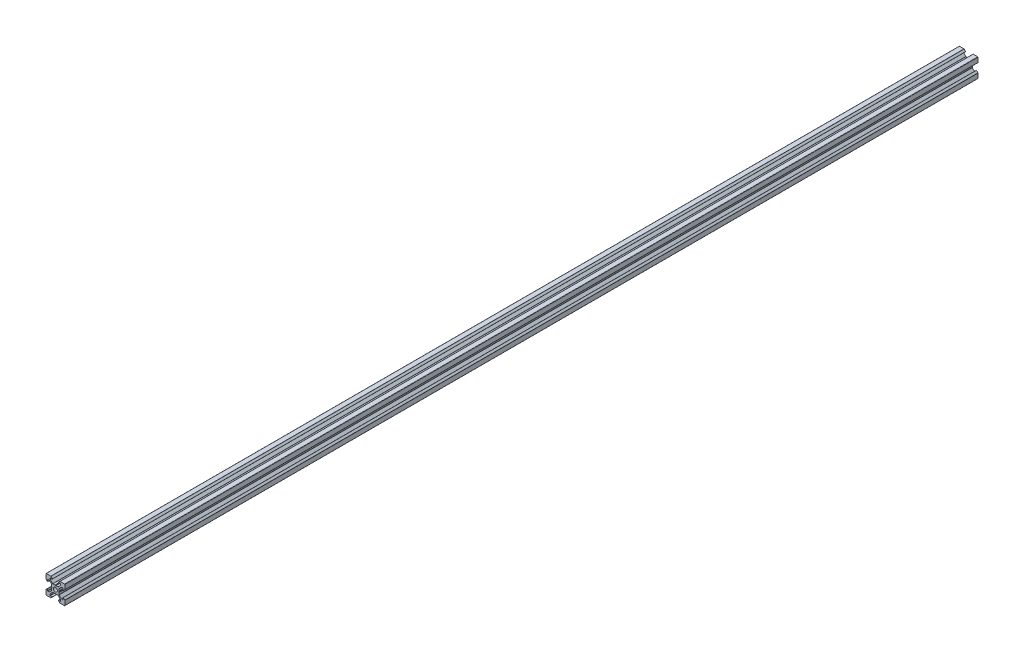
SolidWorks part; units mm, degrees
material "6063-T5"
ref_plane "Plan de face" through (0, 0, 0) normal (0, 0, 1) x (1, 0, 0)
ref_plane "Plan de dessus" through (0, 0, 0) normal (0, 1, 0) x (1, 0, 0)
ref_plane "Plan de droite" through (0, 0, 0) normal (1, 0, 0) x (0, 0, -1)
sketch "Esquisse1" plane through (0, 0, 0) normal (0, 0, 1) x (1, 0, 0)
  line L0 (18.7749, -2.8952) -> (18.7749, -4.8946)
  line L1 (18.4749, -5.1946) -> (17.2591, -5.1946)
  line L2 (17.047, -5.1067) -> (14.5634, -2.6231)
  line L3 (14.4755, -2.411) -> (14.4755, -0.2148)
  line L4 (14.4755, -0.2148) -> (14.1755, 0.3048)
  line L5 (14.1755, 0.3048) -> (14.4755, 0.8244)
  line L6 (14.4755, 0.8244) -> (14.4755, 3.0205)
  line L7 (14.5634, 3.2326) -> (17.047, 5.7162)
  line L8 (17.2591, 5.8041) -> (18.4749, 5.8041)
  line L9 (18.7749, 5.5041) -> (18.7749, 3.5048)
  line L10 (18.9456, 3.4341) -> (20.487, 4.9755)
  line L11 (20.5749, 5.1876) -> (20.5749, 10.0048)
  line L12 (20.2749, 10.3048) -> (15.4577, 10.3048)
  line L13 (15.2456, 10.2169) -> (13.7041, 8.6755)
  line L14 (13.7749, 8.5048) -> (15.7742, 8.5048)
  line L15 (16.0742, 8.2048) -> (16.0742, 6.989)
  line L16 (15.9863, 6.7769) -> (13.5027, 4.2933)
  line L17 (13.2906, 4.2054) -> (11.0945, 4.2054)
  line L18 (11.0945, 4.2054) -> (10.5749, 3.9054)
  line L19 (10.5749, 3.9054) -> (10.0552, 4.2054)
  line L20 (10.0552, 4.2054) -> (7.8591, 4.2054)
  line L21 (7.647, 4.2933) -> (5.1634, 6.7769)
  line L22 (5.0755, 6.989) -> (5.0755, 8.2048)
  line L23 (5.3755, 8.5048) -> (7.3749, 8.5048)
  line L24 (7.4456, 8.6755) -> (5.9041, 10.2169)
  line L25 (5.692, 10.3048) -> (0.8749, 10.3048)
  line L26 (0.5749, 10.0048) -> (0.5749, 5.1876)
  line L27 (0.6627, 4.9755) -> (2.2041, 3.4341)
  line L28 (2.3749, 3.5048) -> (2.3749, 5.5041)
  line L29 (2.6749, 5.8041) -> (3.8906, 5.8041)
  line L30 (4.1027, 5.7162) -> (6.5863, 3.2326)
  line L31 (6.6742, 3.0205) -> (6.6742, 0.8244)
  line L32 (6.6742, 0.8244) -> (6.9742, 0.3048)
  line L33 (6.9742, 0.3048) -> (6.6742, -0.2148)
  line L34 (6.6742, -0.2148) -> (6.6742, -2.411)
  line L35 (6.5863, -2.6231) -> (4.1027, -5.1067)
  line L36 (3.8906, -5.1946) -> (2.6749, -5.1946)
  line L37 (2.3749, -4.8946) -> (2.3749, -2.8952)
  line L38 (2.2041, -2.8245) -> (0.6627, -4.3659)
  line L39 (0.5749, -4.5781) -> (0.5749, -9.3952)
  line L40 (0.8749, -9.6952) -> (5.692, -9.6952)
  line L41 (5.9041, -9.6074) -> (7.4456, -8.0659)
  line L42 (7.3749, -7.8952) -> (5.3755, -7.8952)
  line L43 (5.0755, -7.5952) -> (5.0755, -6.3795)
  line L44 (5.1634, -6.1674) -> (7.647, -3.6838)
  line L45 (7.8591, -3.5959) -> (10.0552, -3.5959)
  line L46 (10.0552, -3.5959) -> (10.5749, -3.2959)
  line L47 (10.5749, -3.2959) -> (11.0945, -3.5959)
  line L48 (11.0945, -3.5959) -> (13.2906, -3.5959)
  line L49 (13.5027, -3.6838) -> (15.9863, -6.1674)
  line L50 (16.0742, -6.3795) -> (16.0742, -7.5952)
  line L51 (15.7742, -7.8952) -> (13.7749, -7.8952)
  line L52 (13.7041, -8.0659) -> (15.2456, -9.6074)
  line L53 (15.4577, -9.6952) -> (20.2749, -9.6952)
  line L54 (20.5749, -9.3952) -> (20.5749, -4.5781)
  line L55 (20.487, -4.3659) -> (18.9456, -2.8245)
  arc A0 (10.5749, -1.7952) -> (12.6749, 0.3048) centre (10.5749, 0.3048) ccw
  arc A1 (12.6749, 0.3048) -> (10.5749, 2.4048) centre (10.5749, 0.3048) ccw
  arc A2 (10.5749, 2.4048) -> (8.4749, 0.3048) centre (10.5749, 0.3048) ccw
  arc A3 (8.4749, 0.3048) -> (10.5749, -1.7952) centre (10.5749, 0.3048) ccw
  arc A4 (18.9456, -2.8245) -> (18.7749, -2.8952) centre (18.8749, -2.8952) ccw
  arc A5 (18.4749, -5.1946) -> (18.7749, -4.8946) centre (18.4749, -4.8946) ccw
  arc A6 (17.047, -5.1067) -> (17.2591, -5.1946) centre (17.2591, -4.8946) ccw
  arc A7 (14.4755, -2.411) -> (14.5634, -2.6231) centre (14.7755, -2.411) ccw
  arc A8 (14.5634, 3.2326) -> (14.4755, 3.0205) centre (14.7755, 3.0205) ccw
  arc A9 (17.2591, 5.8041) -> (17.047, 5.7162) centre (17.2591, 5.5041) ccw
  arc A10 (18.7749, 5.5041) -> (18.4749, 5.8041) centre (18.4749, 5.5041) ccw
  arc A11 (18.7749, 3.5048) -> (18.9456, 3.4341) centre (18.8749, 3.5048) ccw
  arc A12 (20.487, 4.9755) -> (20.5749, 5.1876) centre (20.2749, 5.1876) ccw
  arc A13 (20.5749, 10.0048) -> (20.2749, 10.3048) centre (20.2749, 10.0048) ccw
  arc A14 (15.4577, 10.3048) -> (15.2456, 10.2169) centre (15.4577, 10.0048) ccw
  arc A15 (13.7041, 8.6755) -> (13.7749, 8.5048) centre (13.7749, 8.6048) ccw
  arc A16 (16.0742, 8.2048) -> (15.7742, 8.5048) centre (15.7742, 8.2048) ccw
  arc A17 (15.9863, 6.7769) -> (16.0742, 6.989) centre (15.7742, 6.989) ccw
  arc A18 (13.2906, 4.2054) -> (13.5027, 4.2933) centre (13.2906, 4.5054) ccw
  arc A19 (7.647, 4.2933) -> (7.8591, 4.2054) centre (7.8591, 4.5054) ccw
  arc A20 (5.0755, 6.989) -> (5.1634, 6.7769) centre (5.3755, 6.989) ccw
  arc A21 (5.3755, 8.5048) -> (5.0755, 8.2048) centre (5.3755, 8.2048) ccw
  arc A22 (7.3749, 8.5048) -> (7.4456, 8.6755) centre (7.3749, 8.6048) ccw
  arc A23 (5.9041, 10.2169) -> (5.692, 10.3048) centre (5.692, 10.0048) ccw
  arc A24 (0.8749, 10.3048) -> (0.5749, 10.0048) centre (0.8749, 10.0048) ccw
  arc A25 (0.5749, 5.1876) -> (0.6627, 4.9755) centre (0.8749, 5.1876) ccw
  arc A26 (2.2041, 3.4341) -> (2.3749, 3.5048) centre (2.2749, 3.5048) ccw
  arc A27 (2.6749, 5.8041) -> (2.3749, 5.5041) centre (2.6749, 5.5041) ccw
  arc A28 (4.1027, 5.7162) -> (3.8906, 5.8041) centre (3.8906, 5.5041) ccw
  arc A29 (6.6742, 3.0205) -> (6.5863, 3.2326) centre (6.3742, 3.0205) ccw
  arc A30 (6.5863, -2.6231) -> (6.6742, -2.411) centre (6.3742, -2.411) ccw
  arc A31 (3.8906, -5.1946) -> (4.1027, -5.1067) centre (3.8906, -4.8946) ccw
  arc A32 (2.3749, -4.8946) -> (2.6749, -5.1946) centre (2.6749, -4.8946) ccw
  arc A33 (2.3749, -2.8952) -> (2.2041, -2.8245) centre (2.2749, -2.8952) ccw
  arc A34 (0.6627, -4.3659) -> (0.5749, -4.5781) centre (0.8749, -4.5781) ccw
  arc A35 (0.5749, -9.3952) -> (0.8749, -9.6952) centre (0.8749, -9.3952) ccw
  arc A36 (5.692, -9.6952) -> (5.9041, -9.6074) centre (5.692, -9.3952) ccw
  arc A37 (7.4456, -8.0659) -> (7.3749, -7.8952) centre (7.3749, -7.9952) ccw
  arc A38 (5.0755, -7.5952) -> (5.3755, -7.8952) centre (5.3755, -7.5952) ccw
  arc A39 (5.1634, -6.1674) -> (5.0755, -6.3795) centre (5.3755, -6.3795) ccw
  arc A40 (7.8591, -3.5959) -> (7.647, -3.6838) centre (7.8591, -3.8959) ccw
  arc A41 (13.5027, -3.6838) -> (13.2906, -3.5959) centre (13.2906, -3.8959) ccw
  arc A42 (16.0742, -6.3795) -> (15.9863, -6.1674) centre (15.7742, -6.3795) ccw
  arc A43 (15.7742, -7.8952) -> (16.0742, -7.5952) centre (15.7742, -7.5952) ccw
  arc A44 (13.7749, -7.8952) -> (13.7041, -8.0659) centre (13.7749, -7.9952) ccw
  arc A45 (15.2456, -9.6074) -> (15.4577, -9.6952) centre (15.4577, -9.3952) ccw
  arc A46 (20.2749, -9.6952) -> (20.5749, -9.3952) centre (20.2749, -9.3952) ccw
  arc A47 (20.5749, -4.5781) -> (20.487, -4.3659) centre (20.2749, -4.5781) ccw
extrude "Boss.-Extru.1" add sketch "Esquisse1" along normal blind 970
